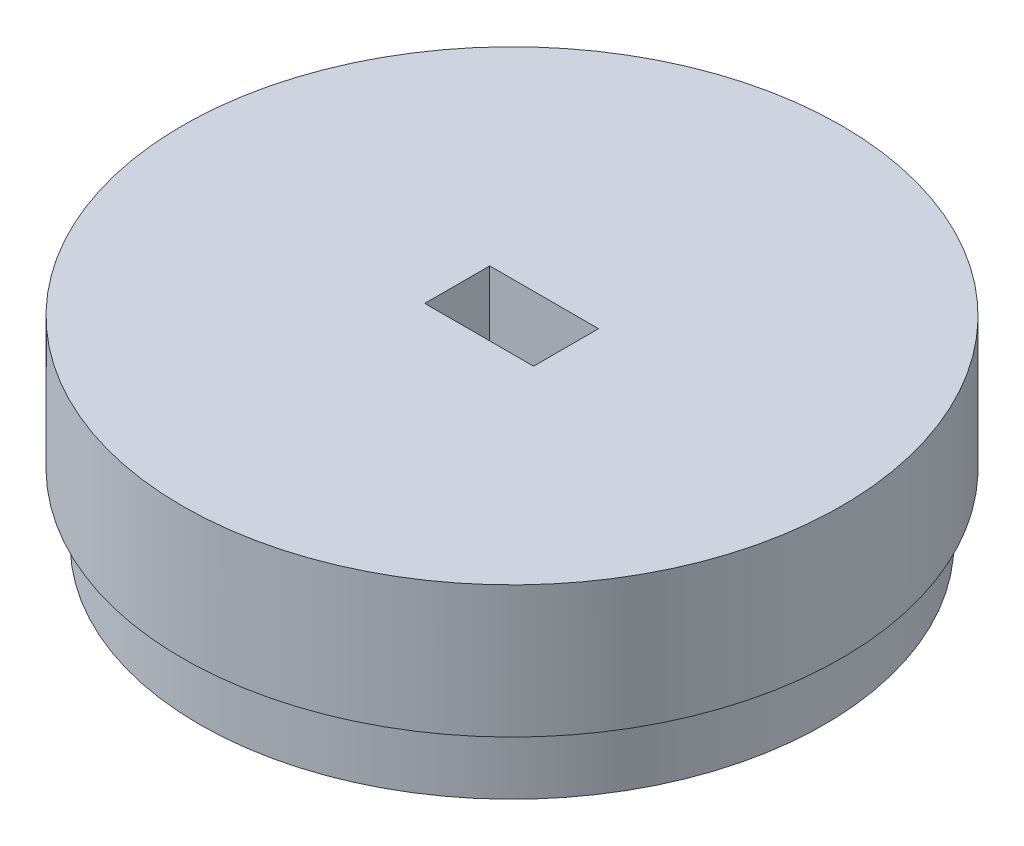
SolidWorks part; units mm, degrees
ref_plane "Front Plane" through (0, 0, 0) normal (0, 0, 1) x (1, 0, 0)
ref_plane "Top Plane" through (0, 0, 0) normal (0, 1, 0) x (1, 0, 0)
ref_plane "Right Plane" through (0, 0, 0) normal (1, 0, 0) x (0, 0, -1)
sketch "Sketch1" plane through (0, 0, 0) normal (0, 1, 0) x (1, 0, 0)
  circle A0 centre (0, 0) radius 15
extrude "Boss-Extrude1" add sketch "Sketch1" along normal blind 9
sketch "Sketch6" plane through (0, 0, 0) normal (0, -1, 0) x (1, 0, 0)
  circle A0 centre (0, 0) radius 14.222
extrude "Cut-Extrude4" cut sketch "Sketch6" along a picked direction on the side against the normal blind 3 flip side to cut contours A0
sketch "Sketch7" plane through (0, 9, 0) normal (0, 1, 0) x (1, 0, 0)
  line L0 (0, 1.492) -> (1.9763, 1.492)
  line L1 (1.9763, 1.492) -> (-1.9763, 1.492)
  line L2 (0, -1.4958) -> (1.9734, -1.4958)
  line L3 (1.9734, -1.4958) -> (0, -1.4958)
  line L4 (-1.9763, -1.492) -> (1.9734, -1.4958)
  circle A0 centre (0, 0) radius 2.4763
  arc A1 (1.9763, 1.492) -> (1.9675, -1.5036) centre (0, 0) ccw
  arc A2 (-1.9763, 1.492) -> (-1.9205, -1.5632) centre (0, 0) ccw
  arc A3 (1.9763, 1.492) -> (1.9108, -1.575) centre (0, 0) ccw
sketch "Sketch8" plane through (0, 9, 0) normal (0, 1, 0) x (1, 0, 0)
  line L1 (2.4763, -1.4958) -> (-2.4763, -1.4958)
  line L2 (2.4763, -1.4958) -> (2.4763, 1.4611)
  line L3 (2.4763, 1.4611) -> (-2.4763, 1.4611)
  line L4 (-2.4763, -1.4958) -> (-2.4763, 1.4611)
extrude "Cut-Extrude5" cut sketch "Sketch8" against normal blind 6
